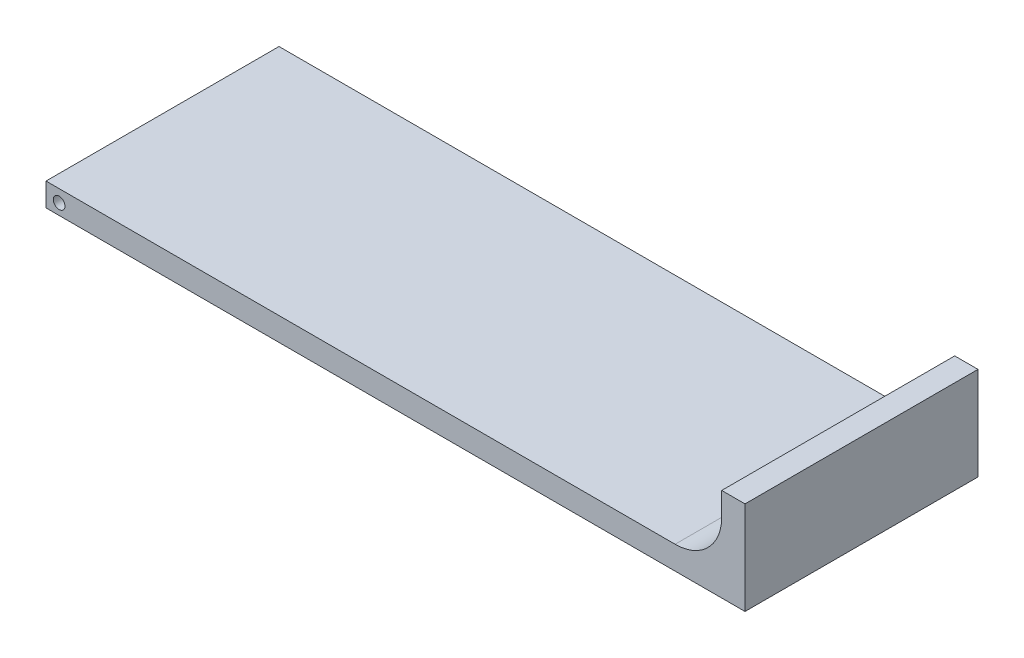
SolidWorks part; units mm, degrees
material "Acrylic (Medium-high impact)"
ref_plane "Front Plane" through (0, 0, 0) normal (0, 0, 1) x (1, 0, 0)
ref_plane "Top Plane" through (0, 0, 0) normal (0, 1, 0) x (1, 0, 0)
ref_plane "Right Plane" through (0, 0, 0) normal (1, 0, 0) x (0, 0, -1)
sketch "Sketch1" plane through (0, 0, 0) normal (0, 0, 1) x (1, 0, 0)
  line L0 (4, 3) -> (5, 3)
  line L1 (5, 3) -> (5, -1)
  line L2 (5, -1) -> (-25, -1)
  line L3 (-25, -1) -> (-25, 0)
  line L4 (-25, 0) -> (4, 0)
  line L5 (4, 0) -> (4, 3)
  point P2 (5, 1)
  dimension "D1" = 30
  dimension "D2" = 25
  dimension "D3" = 1
  dimension "D4" = 4
  dimension "D5" = 1
  dimension "D6" = 1
extrude "Boss-Extrude1" add sketch "Sketch1" along normal blind 10
fillet "Fillet1" radius 2 1 edges at (4, 0, 5)
sketch "Sketch3" plane through (0, 0, 10) normal (0, 0, 1) x (1, 0, 0)
  circle A0 centre (-24.4365, -0.5294) radius 0.25
extrude "Cut-Extrude1" cut sketch "Sketch3" against normal through all
